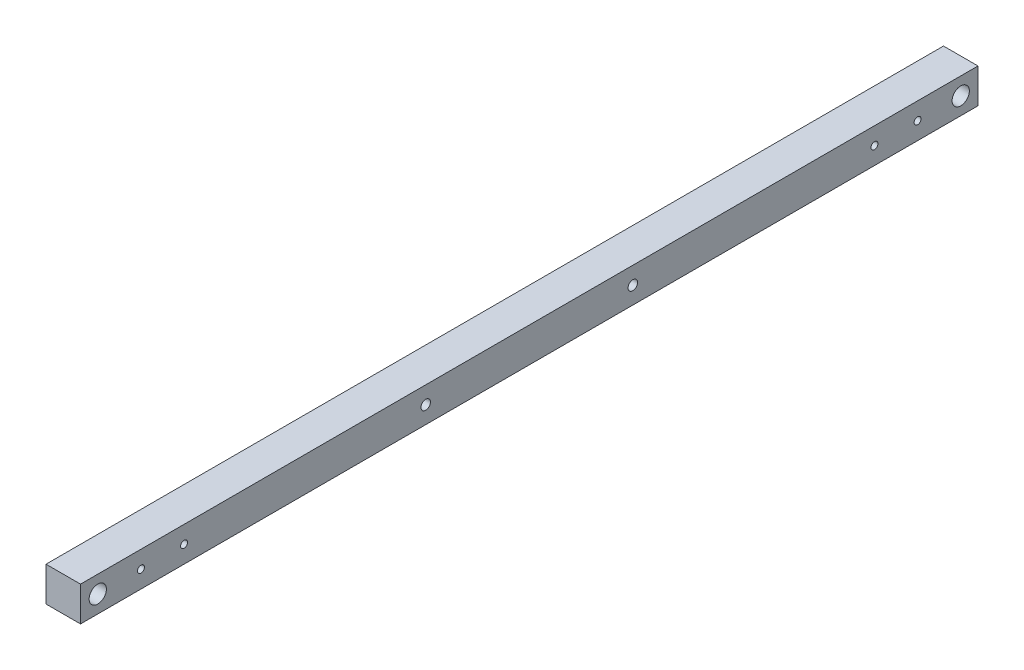
SolidWorks part; units mm, degrees
ref_plane "Front Plane" through (0, 0, 0) normal (0, 0, 1) x (1, 0, 0)
ref_plane "Top Plane" through (0, 0, 0) normal (0, 1, 0) x (1, 0, 0)
ref_plane "Right Plane" through (0, 0, 0) normal (1, 0, 0) x (0, 0, -1)
sketch "Sketch1" plane through (0, 0, 0) normal (0, 0, 1) x (1, 0, 0)
  line L5 (-12.7, -12.7) -> (12.7, -12.7)
  line L6 (-12.7, -12.7) -> (-12.7, 12.7)
  line L7 (-12.7, 12.7) -> (12.7, 12.7)
  line L8 (12.7, -12.7) -> (12.7, 12.7)
  line L9 (-12.7, -12.7) -> (12.7, 12.7) construction
  line L10 (-12.7, 12.7) -> (12.7, -12.7) construction
  point P0 (0, 0)
  dimension "D1" = 25.4
  dimension "D2" = 25.4
extrude "Boss-Extrude1" add sketch "Sketch1" along normal blind 660.4
sketch "Sketch2" plane through (-12.7, 0, 0) normal (1, 0, 0) x (0, 0, -1)
  line L0 (0, 0) -> (-660.4, 0) construction
  line L1 (-660.4, 12.7) -> (-660.4, -12.7) construction
  line L2 (-330.2, 0) -> (-330.2, 46.4779) construction
  line L4 (0, -12.7) -> (0, 12.7) construction
  circle A0 centre (-12.7, 0) radius 6.35
  circle A1 centre (-647.7, 0) radius 6.35
  dimension "D1" = 12.7
  dimension "D2" = 12.7
extrude "Cut-Extrude4" cut sketch "Sketch2" against normal through all and the other way through all contours A1 | A0
sketch "Sketch3" plane through (-12.7, 0, 0) normal (-1, 0, 0) x (0, 0, 1)
  line L0 (660.4, 12.7) -> (660.4, -12.7) construction
  line L1 (660.4, 12.7) -> (0, 12.7) construction
  line L2 (330.2, 12.7) -> (330.2, 76.0207) construction
  circle A0 centre (584.2, 0) radius 2.55
  circle A1 centre (76.2, 0) radius 2.55
  circle A2 centre (615.95, 0) radius 2.55
  circle A4 centre (44.45, 0) radius 2.55
  point P12 (0, 0)
  point P13 (0, 0)
  dimension "D1" = 5.1
  dimension "D2" = 76.2
  dimension "D4" = 5.1
  dimension "D5" = 31.75
  dimension "D3" = 12.7
extrude "Cut-Extrude5" cut sketch "Sketch3" against normal through all
sketch "Sketch10" plane through (-12.7, 0, 0) normal (-1, 0, 0) x (0, 0, 1)
  line L0 (330.2, 12.7) -> (330.2, 75.2381) construction
  line L1 (660.4, 12.7) -> (0, 12.7) construction
  circle A0 centre (406.4, 0) radius 3.5
  circle A1 centre (254, 0) radius 3.5
  dimension "D1" = 7
  dimension "D3" = 76.2
  dimension "D2" = 12.7
extrude "Cut-Extrude6" cut sketch "Sketch10" against normal through all
